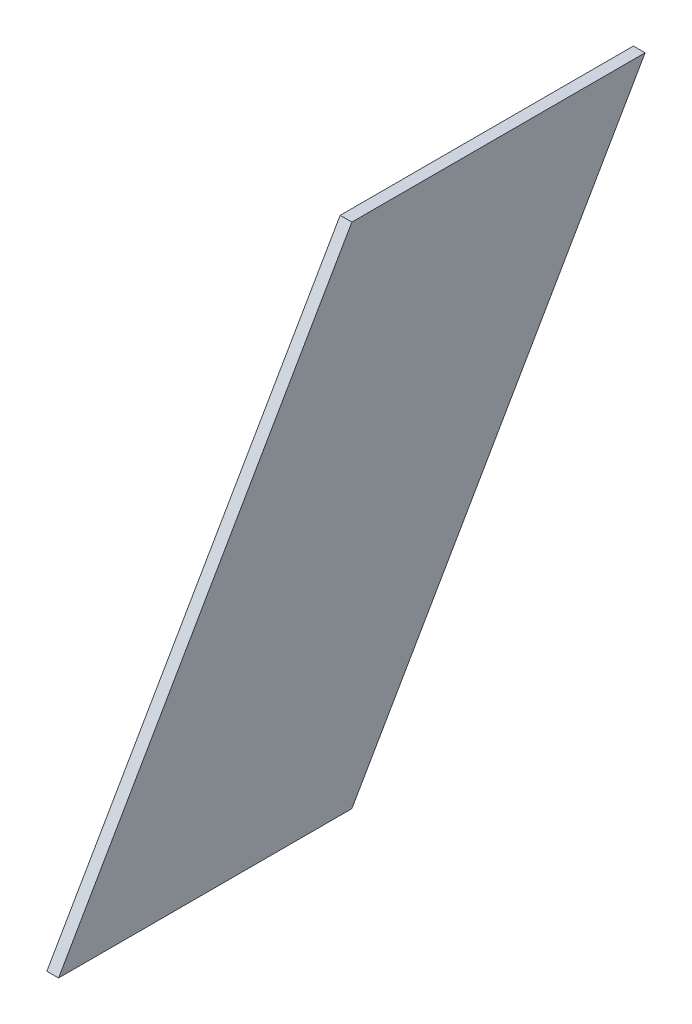
SolidWorks part; units mm, degrees
ref_plane "Front Plane" through (0, 0, 0) normal (0, 0, 1) x (1, 0, 0)
ref_plane "Top Plane" through (0, 0, 0) normal (0, 1, 0) x (1, 0, 0)
ref_plane "Right Plane" through (0, 0, 0) normal (1, 0, 0) x (0, 0, -1)
sketch "Sketch1" plane through (0, 0, 0) normal (1, 0, 0) x (0, 0, -1)
  line L0 (0, 0) -> (50, 0)
  line L1 (0, 0) -> (50, 86.6025)
  line L2 (50, 86.6025) -> (100, 86.6025)
  line L3 (50, 0) -> (100, 86.6025)
extrude "Boss-Extrude1" add sketch "Sketch1" along normal blind 2
sketch "Sketch2" plane through (0, 0, 0) normal (0, -1, 0) x (1, 0, 0)
  line L0 (1, -50) -> (1, 0) construction
  line L1 (2, -50) -> (0, -50) construction
  line L2 (2, 0) -> (0, 0) construction
  circle A0 centre (1, -25) radius 0.5
  dimension "D1" = 25
extrude "Cut-Extrude2" cut sketch "Sketch2" against normal blind 2 contours A0
